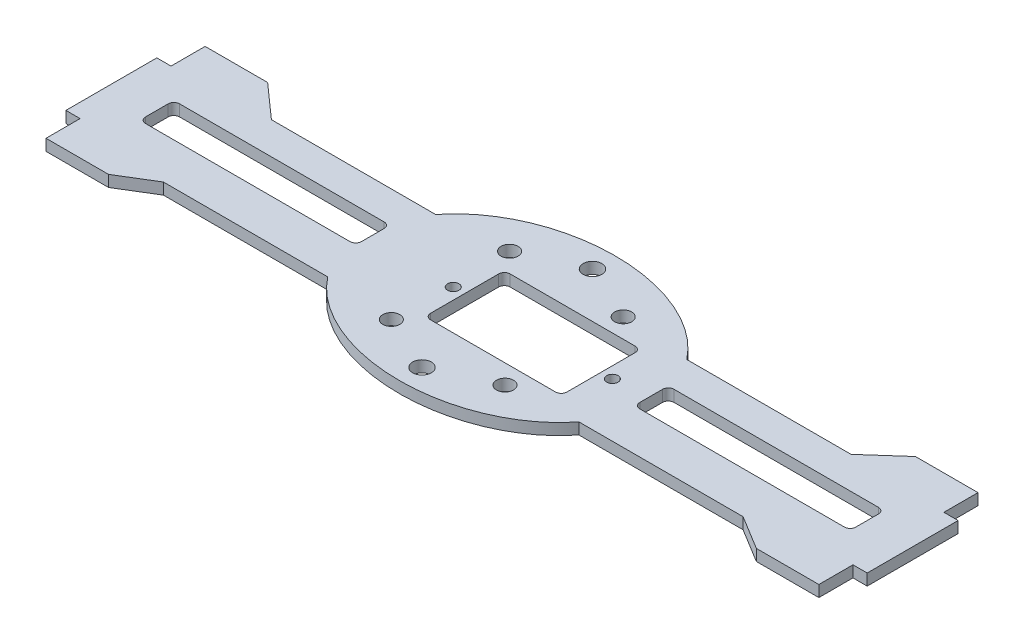
SolidWorks part; units mm, degrees
material "Fibra de Vidro S"
ref_plane "Plano frontal" through (0, 0, 0) normal (0, 0, 1) x (1, 0, 0)
ref_plane "Plano superior" through (0, 0, 0) normal (0, 1, 0) x (1, 0, 0)
ref_plane "Plano direito" through (0, 0, 0) normal (1, 0, 0) x (0, 0, -1)
sketch "Esboço1" plane through (0, 0, 0) normal (0, 1, 0) x (1, 0, 0)
  line L0 (-57, 14.8362) -> (-51, 9.5)
  line L1 (-68, -13.1638) -> (-57, -13.1638)
  line L2 (-68, 14.8362) -> (-68, 8.8362)
  line L3 (-68, 14.8362) -> (-57, 14.8362)
  line L4 (68, -13.1638) -> (68, -7.1638)
  line L5 (-22.0836, 9.5) -> (-51, 9.5)
  line L6 (-22.0836, -9.5) -> (-51, -9.5)
  line L7 (51, 9.5) -> (22.0836, 9.5)
  line L8 (-68, -7.1638) -> (-68, -13.1638)
  line L9 (51, -9.5) -> (22.0836, -9.5)
  line L10 (-68, -7.1638) -> (-70.5, -7.1638)
  line L11 (57, 14.8362) -> (68, 14.8362)
  line L12 (57, -13.1638) -> (68, -13.1638)
  line L13 (-57, -13.1638) -> (-51, -9.5)
  line L14 (57, 14.8362) -> (51, 9.5)
  line L15 (57, -13.1638) -> (51, -9.5)
  line L16 (68, 8.8362) -> (68, 14.8362)
  line L18 (-68, 8.8362) -> (-70.5, 8.8362)
  line L19 (-70.5, -7.1638) -> (-70.5, 8.8362)
  line L23 (68, -7.1638) -> (70.5, -7.1638)
  line L25 (68, 8.8362) -> (70.5, 8.8362)
  line L26 (70.5, -7.1638) -> (70.5, 8.8362)
  ellipse E0 centre (0, 0) end of major axis (25.5, 0) minor radius 19 (-22.0836, -9.5) -> (22.0836, -9.5) ccw
  ellipse E1 centre (0, 0) end of major axis (25.5, 0) minor radius 19 (22.0836, 9.5) -> (-22.0836, 9.5) ccw
  point P0 (0, 0)
  point P6 (0, 0)
  point P7 (-68, 0)
  dimension "D1" = 136
  dimension "D2" = 28
  dimension "D3" = 19
  dimension "D4" = 11
  dimension "D5" = 6
  dimension "D6" = 11
  dimension "D7" = 6
  dimension "D8" = 38
  dimension "D9" = 51
  dimension "D10" = 2.5
  dimension "D11" = 16
  dimension "D12" = 2.5
  dimension "D13" = 16
extrude "Ressalto-extrusão1" add sketch "Esboço1" along normal blind 2
sketch "Esboço2" plane through (0, 2, 0) normal (0, 1, 0) x (1, 0, 0)
  line L0 (70.5, -7.1638) -> (70.5, 8.8362) construction
  line L1 (25.5, 3.8362) -> (61.5, 3.8362)
  line L2 (24.5, 2.8362) -> (24.5, -1.1638)
  line L3 (25.5, -2.1638) -> (61.5, -2.1638)
  line L4 (62.5, 2.8362) -> (62.5, -1.1638)
  line L5 (-61.5, 3.8362) -> (-25.5, 3.8362)
  line L6 (-62.5, 2.8362) -> (-62.5, -1.1638)
  line L7 (-61.5, -2.1638) -> (-25.5, -2.1638)
  line L8 (-24.5, 2.8362) -> (-24.5, -1.1638)
  line L9 (-70.5, 8.8362) -> (-70.5, -7.1638) construction
  line L11 (-6.5, 7) -> (15.5, 7)
  line L12 (-7.5, 6) -> (-7.5, -6)
  line L13 (-6.5, -7) -> (15.5, -7)
  line L14 (16.5, 6) -> (16.5, -6)
  line L15 (-7.5, 7) -> (16.5, -7) construction
  line L16 (-7.5, -7) -> (16.5, 7) construction
  arc A0 (61.5, 3.8362) -> (62.5, 2.8362) centre (61.5, 2.8362) cw
  arc A1 (62.5, -1.1638) -> (61.5, -2.1638) centre (61.5, -1.1638) cw
  arc A2 (25.5, -2.1638) -> (24.5, -1.1638) centre (25.5, -1.1638) cw
  arc A3 (24.5, 2.8362) -> (25.5, 3.8362) centre (25.5, 2.8362) cw
  arc A4 (-25.5, 3.8362) -> (-24.5, 2.8362) centre (-25.5, 2.8362) cw
  arc A5 (-24.5, -1.1638) -> (-25.5, -2.1638) centre (-25.5, -1.1638) cw
  arc A6 (-61.5, -2.1638) -> (-62.5, -1.1638) centre (-61.5, -1.1638) cw
  arc A7 (-62.5, 2.8362) -> (-61.5, 3.8362) centre (-61.5, 2.8362) cw
  arc A8 (16.5, 6) -> (15.5, 7) centre (15.5, 6) ccw
  arc A9 (15.5, -7) -> (16.5, -6) centre (15.5, -6) ccw
  arc A10 (-6.5, -7) -> (-7.5, -6) centre (-6.5, -6) cw
  arc A11 (-7.5, 6) -> (-6.5, 7) centre (-6.5, 6) cw
  circle A12 centre (0, 15) radius 1.65
  circle A13 centre (10, 10.4) radius 1.5
  circle A14 centre (-10, 10.4) radius 1.5
  circle A15 centre (0, -15) radius 1.65
  circle A16 centre (10, -10.4) radius 1.5
  circle A17 centre (-10, -10.4) radius 1.5
  circle A18 centre (-9.5, 0) radius 1
  circle A19 centre (18.5, 0) radius 1
  ellipse E0 centre (0, 0) end of major axis (25.5, 0) minor radius 19 (-22.0836, -9.5) -> (22.0836, -9.5) ccw construction
  ellipse E1 centre (0, 0) end of major axis (25.5, 0) minor radius 19 (22.0836, 9.5) -> (-22.0836, 9.5) ccw construction
  point P0 (44.5, -0.4312)
  point P2 (-42.5, -0.4312)
  point P30 (4.5, 0)
  point P35 (0, -19)
  point P57 (0, 19)
  point P75 (0, -19)
  point P80 (62.5, 0.8362)
  point P81 (70.5, 0.8362)
  point P82 (16.5, 0)
  point P83 (-24.5, 0.8362)
  dimension "D4" = 1
  dimension "D11" = 1
  dimension "D14" = 3.3
  dimension "D15" = 3
  dimension "D21" = 2
  dimension "D1" = 2
  dimension "D2" = 8
  dimension "D3" = 6
  dimension "D5" = 8
  dimension "D6" = 36
  dimension "D7" = 24
  dimension "D8" = 14
  dimension "D9" = 8
  dimension "D10" = 12
  dimension "D12" = 4
  dimension "D13" = 3.4
  dimension "D16" = 10
  dimension "D17" = 10
  dimension "D18" = 3.4
  dimension "D19" = 3.4
  dimension "D20" = 4
  dimension "D22" = 2
  dimension "D23" = 2
extrude "Corte-extrusão1" cut sketch "Esboço2" against normal through all
